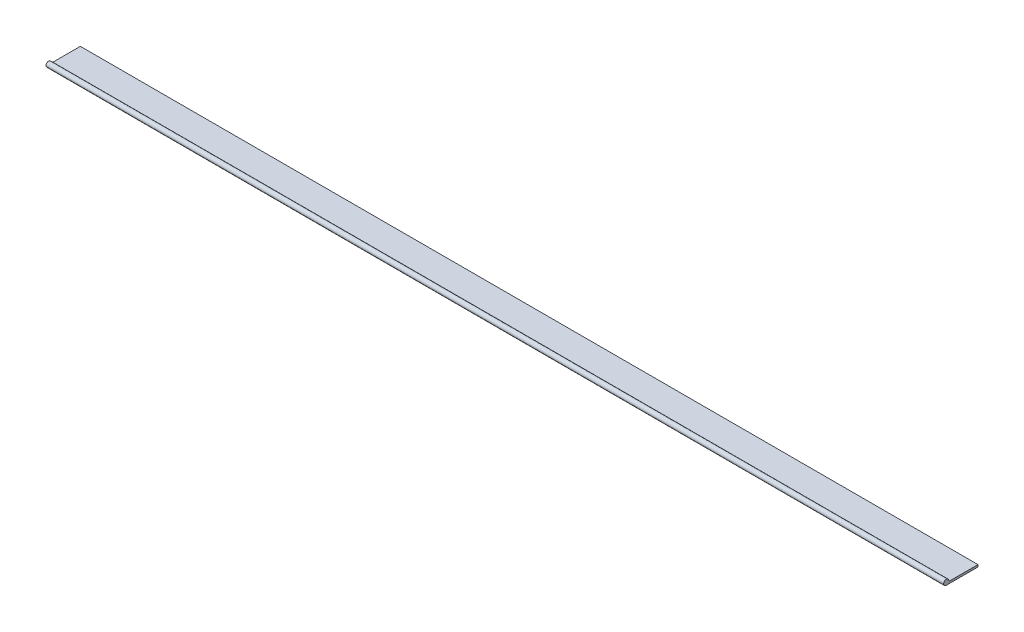
SolidWorks part; units mm, degrees
ref_plane "Front Plane" through (0, 0, 0) normal (0, 0, 1) x (1, 0, 0)
ref_plane "Top Plane" through (0, 0, 0) normal (0, 1, 0) x (1, 0, 0)
ref_plane "Right Plane" through (0, 0, 0) normal (1, 0, 0) x (0, 0, -1)
sketch "Sketch1" plane through (0, 0, 0) normal (1, 0, 0) x (0, 0, -1)
  line L0 (0, 0) -> (9.652, 0)
  line L1 (9.652, 0) -> (9.652, 0.635)
  line L2 (9.652, 0.635) -> (0.7777, 0.635)
  arc A0 (0.7777, 0.635) -> (0, 0) centre (0, 0.7937) ccw
  dimension "D1" = 0.635
  dimension "D2" = 1.5875
  dimension "D3" = 9.652
extrude "Boss-Extrude1" add sketch "Sketch1" along normal blind 273.05
